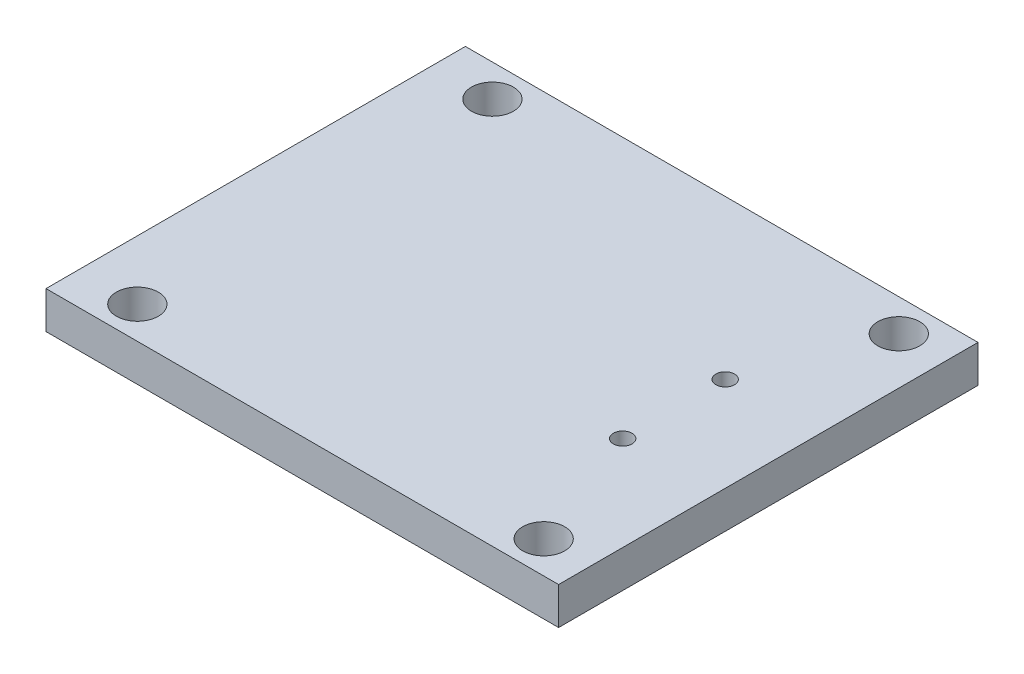
SolidWorks part; units mm, degrees
material "E-Glass Fiber"
ref_plane "Front Plane" through (0, 0, 0) normal (0, 0, 1) x (1, 0, 0)
ref_plane "Top Plane" through (0, 0, 0) normal (0, 1, 0) x (1, 0, 0)
ref_plane "Right Plane" through (0, 0, 0) normal (1, 0, 0) x (0, 0, -1)
sketch "Sketch1" plane through (0, 0, 0) normal (0, 1, 0) x (1, 0, 0)
  line L0 (0, 7.62) -> (6.78, 7.62) construction
  line L1 (6.78, 16.62) -> (28.78, 16.62)
  line L2 (6.78, 16.62) -> (6.78, -1.38)
  line L3 (6.78, -1.38) -> (28.78, -1.38)
  line L4 (28.78, 16.62) -> (28.78, -1.38)
  line L5 (0, 0) -> (35.56, 0) construction
  line L6 (0, 0) -> (0, 15.24) construction
  line L7 (0, 15.24) -> (35.56, 15.24) construction
  line L8 (35.56, 0) -> (35.56, 15.24) construction
  line L10 (35.56, 7.62) -> (28.78, 7.62) construction
  dimension "D1" = 22
  dimension "D2" = 18
  dimension "D3" = 15.24
  dimension "D4" = 35.56
extrude "Boss-Extrude2" add sketch "Sketch1" along normal blind 1.6
sketch "Sketch4" plane through (0, 0, 0) normal (0, 1, 0) x (1, 0, 0)
  line L0 (-0.88, 0) -> (0.88, 0) construction
  line L2 (6.78, 16.62) -> (6.78, -1.38) construction
  circle A0 centre (26.76, 15.24) radius 0.9
  circle A1 centre (26.76, 0) radius 0.9
  circle A2 centre (9.32, 0) radius 0.9
  circle A3 centre (9.32, 15.24) radius 0.9
  point P10 (8.1812, 0)
  dimension "D3" = 1.8
  dimension "D1" = 17.44
  dimension "D2" = 2.54
  dimension "D4" = 15.24
  dimension "D5" = 15.24
extrude "Cut-Extrude5" cut sketch "Sketch4" along normal blind 1.6
sketch "Sketch5" plane through (0, 1.6, 0) normal (0, 1, 0) x (1, 0, 0)
  circle A0 centre (26.76, 15.24) radius 0.9
  circle A1 centre (26.76, 15.24) radius 1.275
  circle A2 centre (26.76, 15.24) radius 0.9 construction
  circle A3 centre (26.76, 0) radius 0.9
  circle A4 centre (26.76, 0) radius 0.9 construction
  circle A5 centre (26.76, 0) radius 1.275
  circle A6 centre (9.32, 15.24) radius 0.9
  circle A7 centre (9.32, 15.24) radius 1.275
  circle A8 centre (9.32, 0) radius 0.9
  circle A9 centre (9.32, 0) radius 1.275
  circle A10 centre (9.32, 15.24) radius 0.9 construction
  circle A11 centre (9.32, 0) radius 0.9 construction
  dimension "D1" = 2.55
extrude "Boss-Extrude3" [suppressed] add sketch "Sketch5" along normal blind 0.1
sketch "Sketch6" plane through (0, 0, 0) normal (1, 0, 0) x (0, 0, -1)
  line L0 (0, 1.6) -> (0.9, 1.6)
  line L1 (-1.38, 1.6) -> (16.62, 1.6) construction
  line L2 (0.2252, 3.1) -> (0, 3.1)
  line L3 (0, 0.88) -> (0, -0.88) construction
  line L4 (0, 3.1) -> (0, 1.6)
  line L5 (0, 1.3722) -> (0, 3.4408) construction
  arc A0 (0.9, 1.6) -> (0.7139, 2.2122) centre (-0.2, 1.6) ccw
  arc A1 (0.7139, 2.2122) -> (0.4221, 2.9352) centre (2.2924, 3.2697) cw
  arc A2 (0.4221, 2.9352) -> (0.2252, 3.1) centre (0.2252, 2.9) ccw
  point P16 (0.4, 3.1)
  dimension "D4" = 1.1
  dimension "D5" = 1.9
  dimension "D6" = 0.2
  dimension "D1" = 1.5
  dimension "D2" = 0.8
  dimension "D3" = 1.8
revolve "Revolve1" [suppressed] add sketch "Sketch6" angle 360 about L5
pattern_linear "LPattern2" [suppressed] count 2 spacing 15.24 count 15 spacing 2.54
ref_plane "Plane3" through (0, 0, -5.08) normal (0, 0, 1) x (1, 0, 0)
sketch "Sketch7" plane through (0, 0, -5.08) normal (0, 0, 1) x (1, 0, 0)
  line L0 (0.127, 3.889) -> (0.127, -2.5597) construction
  line L2 (0, -1.705) -> (0, 1.705) construction
  line L3 (0.127, 0) -> (1.027, 0)
  line L4 (9.9, 0) -> (-9.9, 0) construction
  line L5 (0.127, 0) -> (0.127, -1.5)
  line L6 (0.127, -1.5) -> (0.3395, -1.5)
  arc A0 (0.538, -1.325) -> (0.807, -0.66) centre (1.927, -1.5) cw
  arc A1 (0.807, -0.66) -> (1.027, 0) centre (-0.073, 0) ccw
  arc A2 (0.3395, -1.5) -> (0.538, -1.325) centre (0.3395, -1.3) ccw
  point P16 (0.527, -1.5)
  dimension "D5" = 1.1
  dimension "D6" = 0.2
  dimension "D1" = 0.127
  dimension "D2" = 1.5
  dimension "D3" = 0.8
  dimension "D4" = 1.8
revolve "Revolve2" [suppressed] add sketch "Sketch7" angle 360 about L0
pattern_linear "LPattern3" [suppressed] count 2 spacing 2.54 count 3 spacing 2.54
sketch "Sketch8" plane through (0, 0, 0) normal (0, -1, 0) x (1, 0, 0)
  circle A0 centre (26.76, 0) radius 0.9
  circle A1 centre (26.76, 0) radius 1.275
  circle A2 centre (26.76, -15.24) radius 1.275
  circle A3 centre (26.76, -15.24) radius 0.9
  circle A4 centre (26.76, -15.24) radius 0.9 construction
  circle A5 centre (26.76, 0) radius 0.9 construction
  circle A6 centre (9.32, 0) radius 0.9
  circle A7 centre (9.32, 0) radius 1.275
  circle A8 centre (9.32, -15.24) radius 0.9
  circle A9 centre (9.32, -15.24) radius 1.275
  circle A10 centre (9.32, 0) radius 0.9 construction
  circle A11 centre (9.32, -15.24) radius 0.9 construction
  dimension "D1" = 2.55
extrude "Boss-Extrude4" [suppressed] add sketch "Sketch8" along normal blind 0.1
sketch "Sketch9" plane through (0, 0, 0) normal (0, 1, 0) x (1, 0, 0)
  line L0 (-0.88, 0) -> (0.88, 0) construction
  line L1 (28.78, -1.38) -> (28.78, 16.62) construction
  circle A0 centre (24.73, 5.42) radius 0.4
  circle A1 centre (24.73, 9.82) radius 0.4
  dimension "D1" = 0.8
  dimension "D2" = 4.4
  dimension "D3" = 5.42
  dimension "D4" = 4.05
extrude "Cut-Extrude6" cut sketch "Sketch9" along normal blind 10
